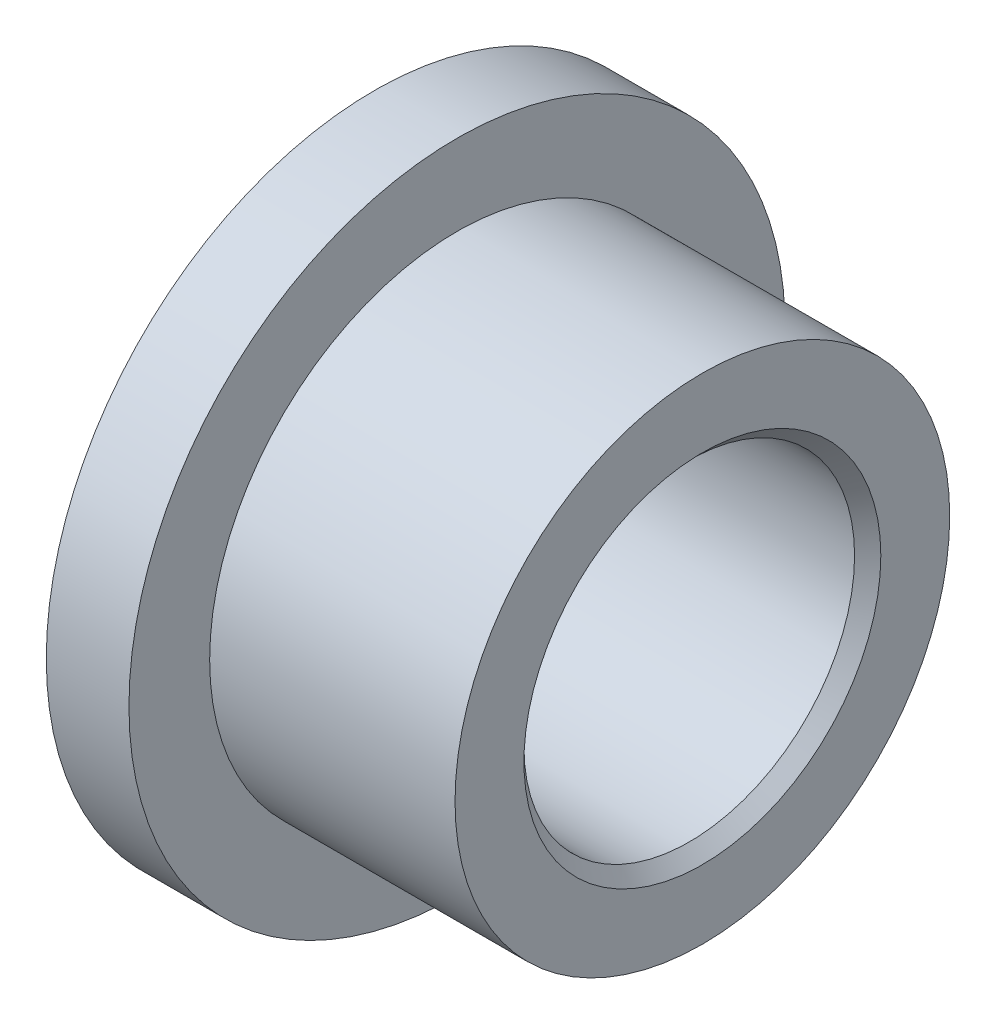
SolidWorks part; units mm, degrees
ref_plane "Front Plane" through (0, 0, 0) normal (0, 0, 1) x (1, 0, 0)
ref_plane "Top Plane" through (0, 0, 0) normal (0, 1, 0) x (1, 0, 0)
ref_plane "Right Plane" through (0, 0, 0) normal (1, 0, 0) x (0, 0, -1)
sketch "Sketch1" plane through (0, 0, 0) normal (1, 0, 0) x (0, 0, -1)
  circle A0 centre (0, 0) radius 3.2004
  circle A1 centre (0, 0) radius 4.7879
  dimension "D1" = 6.4008
  dimension "D2" = 9.5758
extrude "Boss-Extrude1" add sketch "Sketch1" along normal blind 4.7498
sketch "Sketch2" plane through (0, 0, 0) normal (-1, 0, 0) x (0, 0, 1)
  circle A0 centre (0, 0) radius 3.2004
  circle A1 centre (0, 0) radius 6.35
  dimension "D1" = 6.4008
  dimension "D2" = 12.7
extrude "Boss-Extrude2" add sketch "Sketch2" along normal blind 1.6002
chamfer "Chamfer1" distance 0.254 angle 45 2 edges at (4.7498, 0, -3.2004) (-1.6002, 0, 3.2004)
